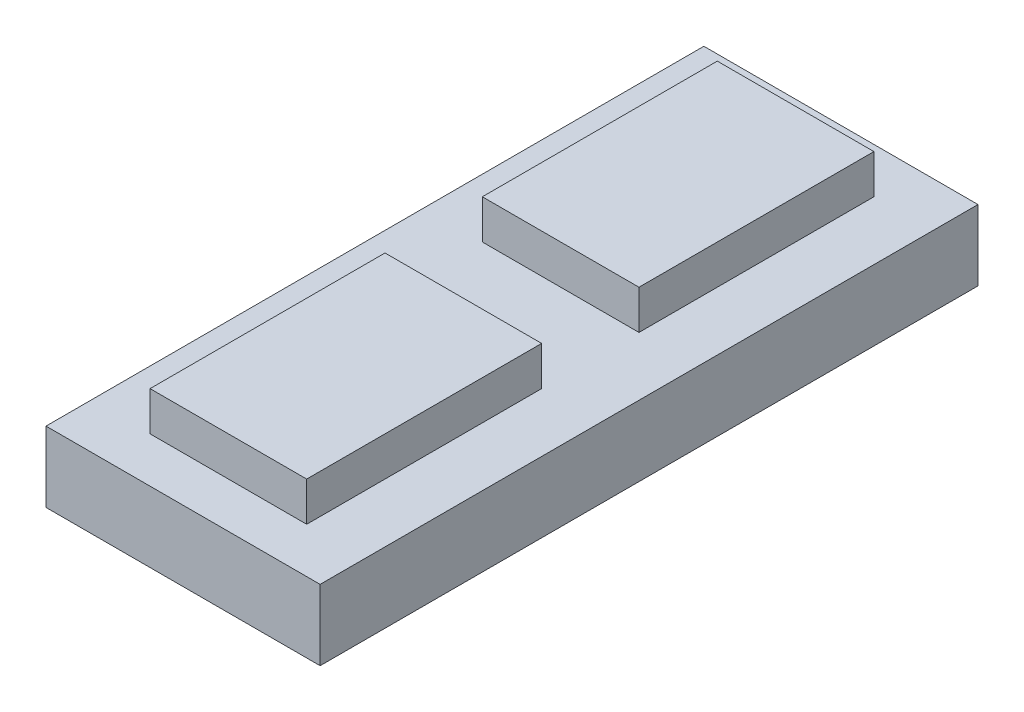
SolidWorks part; units mm, degrees
ref_plane "Front Plane" through (0, 0, 0) normal (0, 0, 1) x (1, 0, 0)
ref_plane "Top Plane" through (0, 0, 0) normal (0, 1, 0) x (1, 0, 0)
ref_plane "Right Plane" through (0, 0, 0) normal (1, 0, 0) x (0, 0, -1)
sketch "Sketch1" plane through (0, 0, 0) normal (0, 1, 0) x (1, 0, 0)
  line L1 (-17.5, 42) -> (17.5, 42)
  line L2 (-17.5, 42) -> (-17.5, -42)
  line L3 (-17.5, -42) -> (17.5, -42)
  line L4 (17.5, 42) -> (17.5, -42)
  line L5 (-17.5, 42) -> (17.5, -42) construction
  line L6 (-17.5, -42) -> (17.5, 42) construction
  point P0 (0, 0)
  dimension "D1" = 84
  dimension "D2" = 35
extrude "Boss-Extrude1" add sketch "Sketch1" along normal blind 9
sketch "Sketch2" plane through (0, 9, 0) normal (0, 1, 0) x (1, 0, 0)
  line L1 (-10, 36.2132) -> (10, 36.2132)
  line L2 (-10, 36.2132) -> (-10, -36.2132)
  line L3 (-10, -36.2132) -> (10, -36.2132)
  line L4 (10, 36.2132) -> (10, -36.2132)
  line L5 (-10, 36.2132) -> (10, -36.2132) construction
  line L6 (-10, -36.2132) -> (10, 36.2132) construction
  line L7 (-10, 6.2132) -> (10, 6.2132)
  line L8 (-10, 6.2132) -> (-10, -6.2132)
  line L9 (-10, -6.2132) -> (10, -6.2132)
  line L10 (10, 6.2132) -> (10, -6.2132)
  line L11 (-10, 6.2132) -> (10, -6.2132) construction
  line L12 (-10, -6.2132) -> (10, 6.2132) construction
  point P0 (0, 0)
  point P6 (0, 0)
  dimension "D1" = 30
  dimension "D2" = 20
extrude "Boss-Extrude2" add sketch "Sketch2" along normal blind 5 separate body contours L2 L7 L4 L1 | L9 L2 L3 L4
